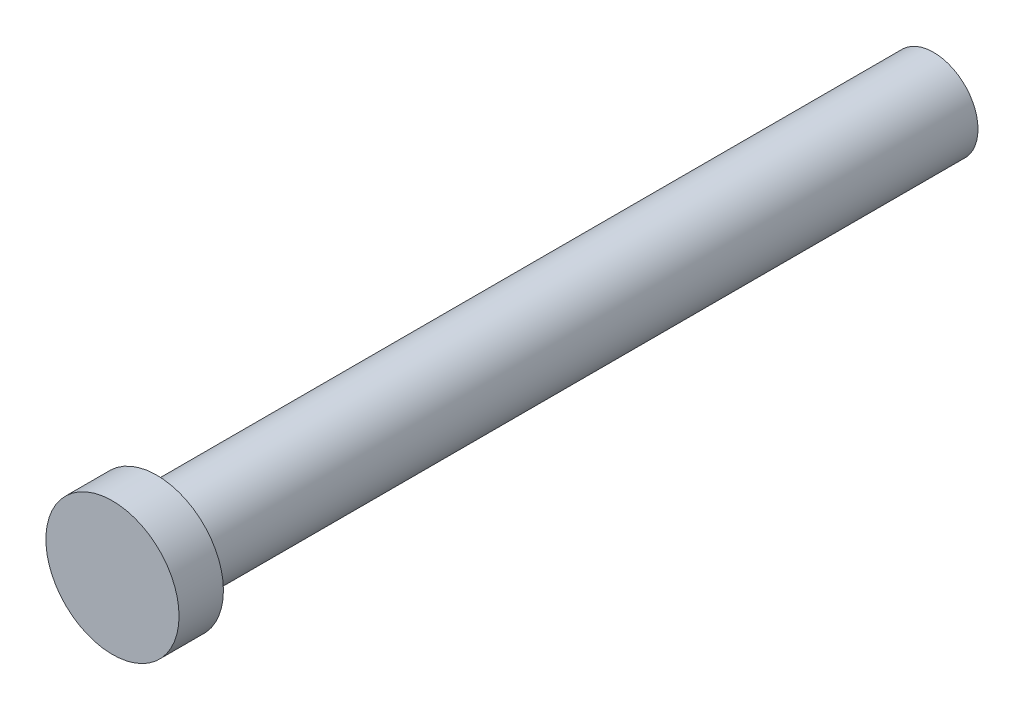
SolidWorks part; units mm, degrees
ref_plane "Front Plane" through (0, 0, 0) normal (0, 0, 1) x (1, 0, 0)
ref_plane "Top Plane" through (0, 0, 0) normal (0, 1, 0) x (1, 0, 0)
ref_plane "Right Plane" through (0, 0, 0) normal (1, 0, 0) x (0, 0, -1)
sketch "Sketch1" plane through (0, 0, 0) normal (0, 0, 1) x (1, 0, 0)
  circle A0 centre (0, 0) radius 2
  dimension "D1" = 4
extrude "Boss-Extrude2" add sketch "Sketch1" along normal blind 35
sketch "Sketch3" plane through (0, 0, 35) normal (0, 0, 1) x (1, 0, 0)
  circle A0 centre (0, 0) radius 3
  dimension "D1" = 6
extrude "Boss-Extrude3" add sketch "Sketch3" along normal blind 2
